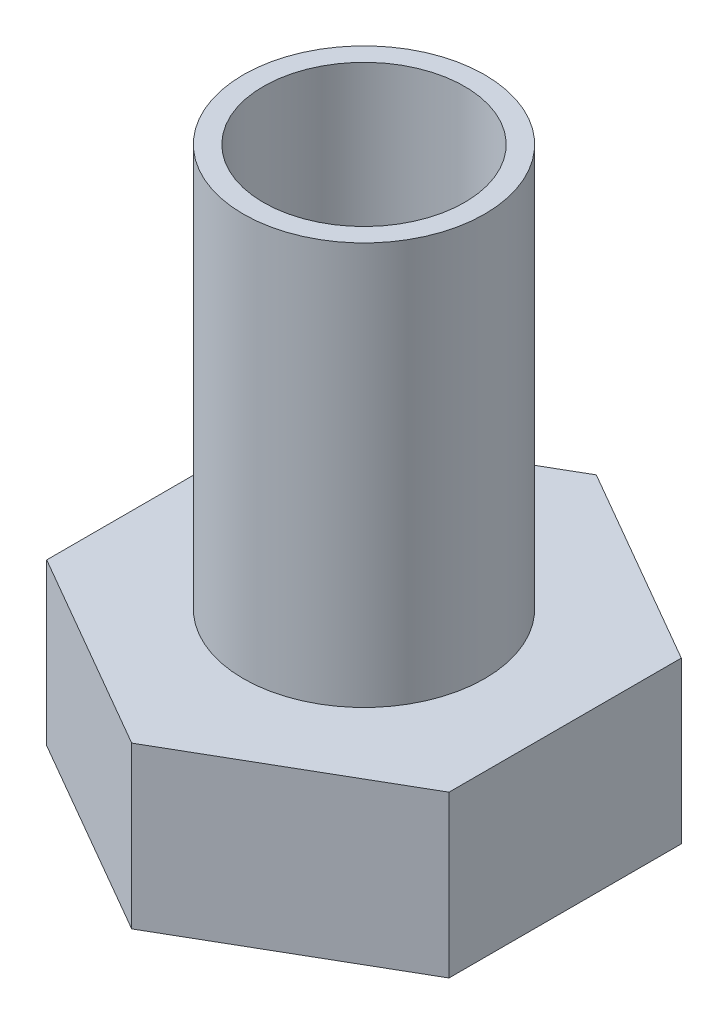
SolidWorks part; units mm, degrees
ref_plane "Front Plane" through (0, 0, 0) normal (0, 0, 1) x (1, 0, 0)
ref_plane "Top Plane" through (0, 0, 0) normal (0, 1, 0) x (1, 0, 0)
ref_plane "Right Plane" through (0, 0, 0) normal (1, 0, 0) x (0, 0, -1)
sketch "Sketch1" plane through (0, 0, 0) normal (0, 1, 0) x (1, 0, 0)
  circle A0 centre (0, 0) radius 3
  circle A1 centre (0, 0) radius 2.5
extrude "Boss-Extrude1" add sketch "Sketch1" along normal blind 10
sketch "Sketch2" plane through (0, 0, 0) normal (0, -1, 0) x (1, 0, 0)
  line L1 (0, 5.7735) -> (-5, 2.8868)
  line L2 (-5, 2.8868) -> (-5, -2.8868)
  line L3 (-5, -2.8868) -> (0, -5.7735)
  line L4 (0, -5.7735) -> (5, -2.8868)
  line L5 (5, -2.8868) -> (5, 2.8868)
  line L6 (5, 2.8868) -> (0, 5.7735)
  circle A0 centre (0, 0) radius 5 construction
extrude "Boss-Extrude2" add sketch "Sketch2" along normal blind 4
